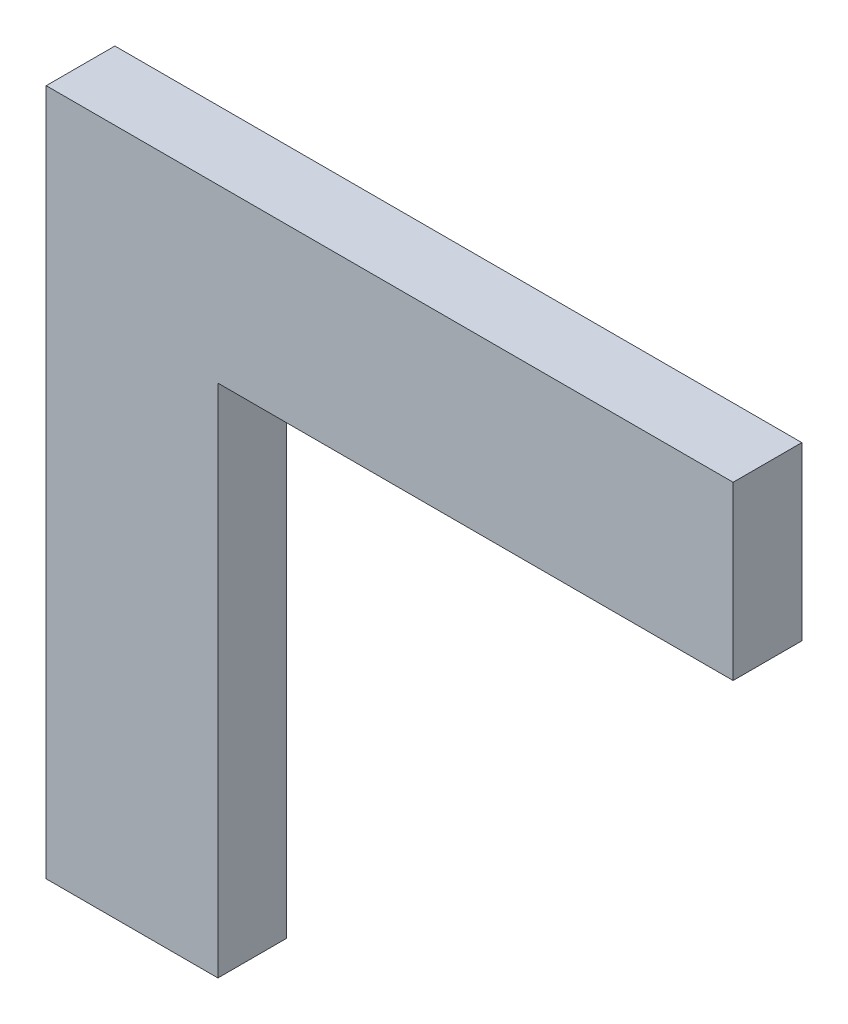
SolidWorks part; units mm, degrees
ref_plane "Plan de face" through (0, 0, 0) normal (0, 0, 1) x (1, 0, 0)
ref_plane "Plan de dessus" through (0, 0, 0) normal (0, 1, 0) x (1, 0, 0)
ref_plane "Plan de droite" through (0, 0, 0) normal (1, 0, 0) x (0, 0, -1)
sketch "Esquisse1" plane through (0, 0, 0) normal (0, 0, 1) x (1, 0, 0)
  line L0 (0, 0) -> (0, 60)
  line L1 (0, 60) -> (60, 60)
  line L2 (60, 60) -> (60, 80)
  line L3 (60, 80) -> (-20, 80)
  line L4 (-20, 80) -> (-20, 0)
  line L5 (-20, 0) -> (0, 0)
  dimension "D1" = 60
  dimension "D2" = 60
  dimension "D3" = 20
  dimension "D4" = 20
extrude "Boss.-Extru.1" add sketch "Esquisse1" along normal blind 8
